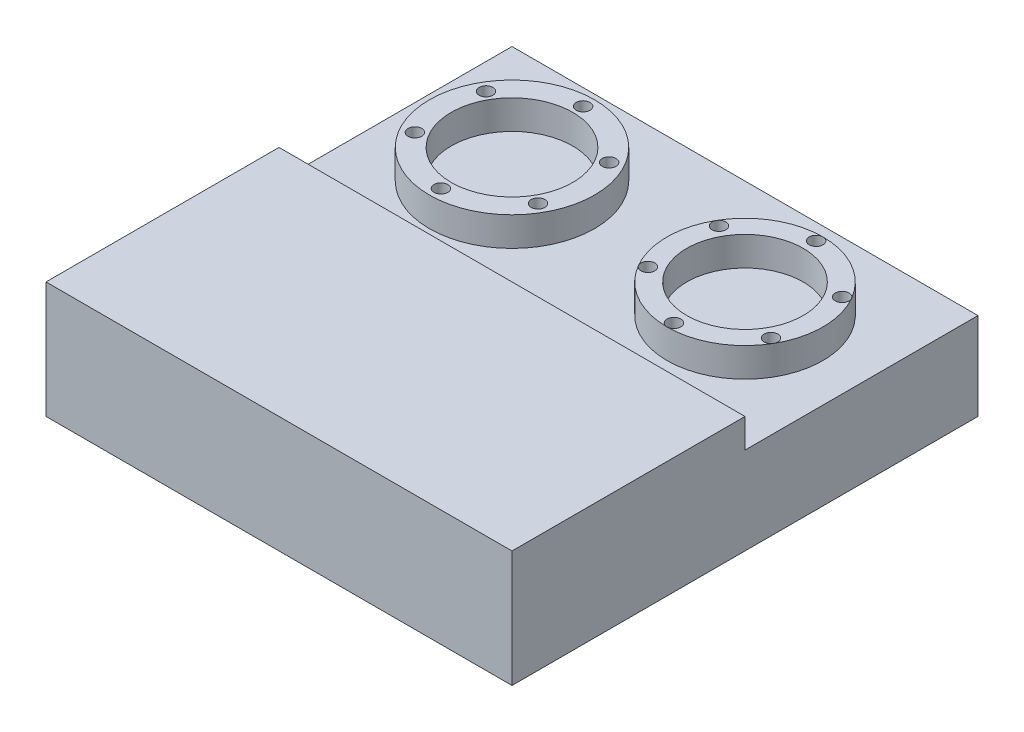
SolidWorks part; units mm, degrees
ref_plane "Front Plane" through (0, 0, 0) normal (0, 0, 1) x (1, 0, 0)
ref_plane "Top Plane" through (0, 0, 0) normal (0, 1, 0) x (1, 0, 0)
ref_plane "Right Plane" through (0, 0, 0) normal (1, 0, 0) x (0, 0, -1)
sketch "Sketch1" plane through (0, 0, 0) normal (0, 1, 0) x (1, 0, 0)
  line L1 (50.8, -50.8) -> (-50.8, -50.8)
  line L2 (50.8, -50.8) -> (50.8, 50.8)
  line L3 (50.8, 50.8) -> (-50.8, 50.8)
  line L4 (-50.8, -50.8) -> (-50.8, 50.8)
  line L5 (50.8, -50.8) -> (-50.8, 50.8) construction
  line L6 (50.8, 50.8) -> (-50.8, -50.8) construction
  point P0 (0, 0)
  dimension "D1" = 101.6
  dimension "D2" = 101.6
extrude "Boss-Extrude1" add sketch "Sketch1" along normal blind 19.05
sketch "Sketch2" plane through (0, 19.05, 0) normal (0, 1, 0) x (1, 0, 0)
  line L0 (-50.8, 50.8) -> (-50.8, -50.8) construction
  line L1 (50.8, 50.8) -> (-50.8, 50.8) construction
  line L2 (50.8, -50.8) -> (50.8, 50.8) construction
  circle A0 centre (-25.4, 25.4) radius 18
  circle A1 centre (-25.4, 25.4) radius 13.25
  circle A2 centre (25.4, 25.4) radius 17.005
  circle A3 centre (25.4, 25.4) radius 12.7
  circle A4 centre (25.4, 40.9) radius 1.5
  circle A5 centre (-25.4, 40.9) radius 1.5
  circle A6 centre (-25.4, 25.4) radius 15.5 construction
  circle A7 centre (25.4, 25.4) radius 15.5 construction
  circle A8 centre (-11.9766, 33.15) radius 1.5
  circle A9 centre (-11.9766, 17.65) radius 1.5
  circle A10 centre (-25.4, 9.9) radius 1.5
  circle A11 centre (-38.8234, 17.65) radius 1.5
  circle A12 centre (-38.8234, 33.15) radius 1.5
  circle A13 centre (38.8234, 33.15) radius 1.5
  circle A14 centre (25.4, 25.4) radius 12.7
  circle A15 centre (38.8234, 17.65) radius 1.5
  circle A16 centre (25.4, 25.4) radius 12.7
  circle A17 centre (25.4, 9.9) radius 1.5
  circle A18 centre (25.4, 25.4) radius 12.7
  circle A19 centre (11.9766, 17.65) radius 1.5
  circle A20 centre (25.4, 25.4) radius 12.7
  circle A21 centre (11.9766, 33.15) radius 1.5
  circle A22 centre (25.4, 25.4) radius 12.7
  point P14 (0, 0)
  point P24 (0, 0)
  point P39 (0, 0)
  point P40 (0, 0)
  dimension "D1" = 3
  dimension "D2" = 3
  dimension "D3" = 26.5
  dimension "D4" = 31
  dimension "D5" = 36
  dimension "D6" = 25.4
  dimension "D7" = 31
  dimension "D8" = 34.01
  dimension "D11" = 25.4
  dimension "D12" = 25.4
  dimension "D13" = 25.4
  dimension "D9" = 6
  dimension "D10" = 6
extrude "Boss-Extrude2" add sketch "Sketch2" along normal blind 6.35 contours A0 A12 A11 A10 A9 A8 A5 A1 | A2 A21 A19 A17 A15 A13 A4 A3
sketch "Sketch3" plane through (0, 19.05, 0) normal (0, 1, 0) x (1, 0, 0)
  line L0 (50.8, -50.8) -> (50.8, 50.8) construction
  line L1 (-50.8, -50.8) -> (50.8, -50.8)
  line L2 (-50.8, -50.8) -> (-50.8, 0)
  line L3 (-50.8, 0) -> (50.8, 0)
  line L4 (50.8, -50.8) -> (50.8, 0)
  dimension "D1" = 50.8
extrude "Boss-Extrude3" add sketch "Sketch3" along normal blind 6.35
